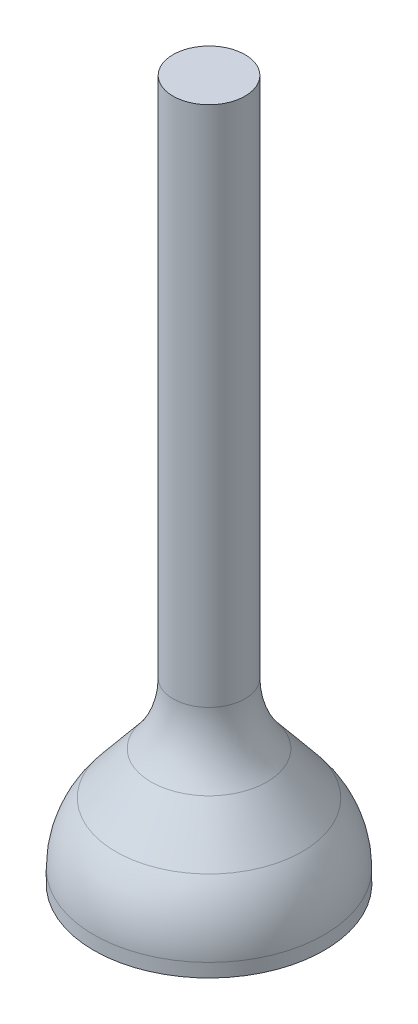
SolidWorks part; units mm, degrees
ref_plane "Front Plane" through (0, 0, 0) normal (0, 0, 1) x (1, 0, 0)
ref_plane "Top Plane" through (0, 0, 0) normal (0, 1, 0) x (1, 0, 0)
ref_plane "Right Plane" through (0, 0, 0) normal (1, 0, 0) x (0, 0, -1)
sketch "Sketch1" plane through (0, 0, 0) normal (0, 1, 0) x (1, 0, 0)
  circle A0 centre (0, 0) radius 3.048
extrude "Boss-Extrude1" add sketch "Sketch1" along normal blind 1.27
ref_plane "Plane1" through (0, 3.81, 0) normal (0, 1, 0) x (1, 0, 0)
sketch "Sketch2" plane through (0, 3.81, 0) normal (0, 1, 0) x (1, 0, 0)
  circle A0 centre (0, 0) radius 0.9525
loft "Loft1" add profiles "Sketch2" section "Sketch2" section edge at (0, 1.27, 3.048)
sketch "Sketch3" plane through (0, 3.81, 0) normal (0, 1, 0) x (1, 0, 0)
  circle A0 centre (0, 0) radius 0.9525
extrude "Boss-Extrude2" add sketch "Sketch3" along normal blind 14.732
fillet "Fillet1" radius 2.54 2 edges at (0, 1.27, 3.048) (0, 3.81, 0.9525)
